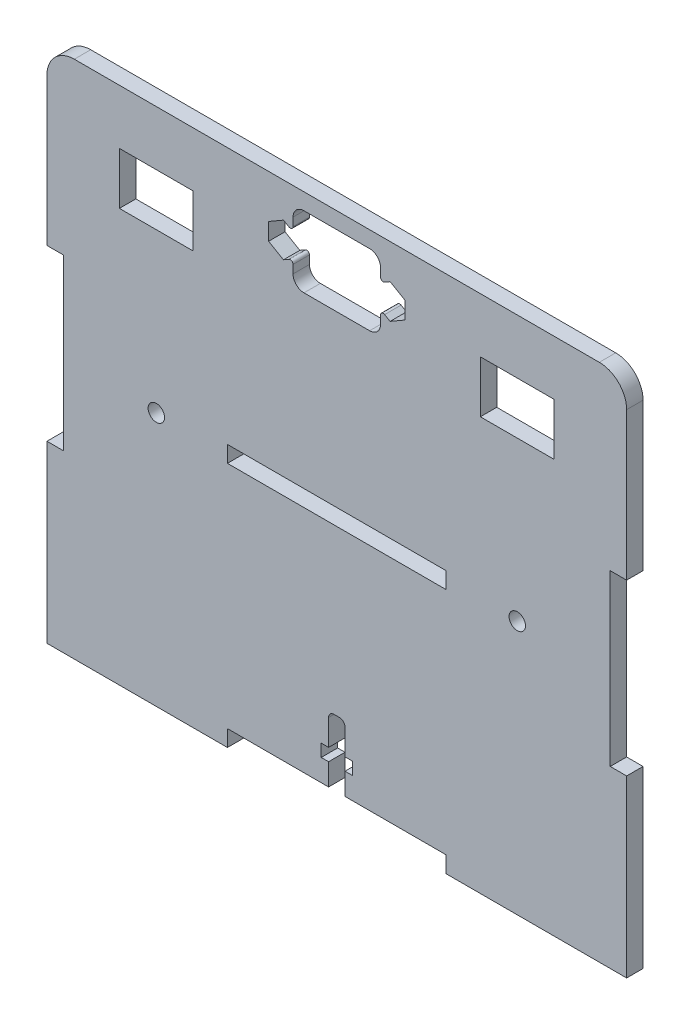
SolidWorks part; units mm, degrees
other "Marcação1"
sketch "Esboço7" plane through (-68, 31.5, 3) normal (-0.6758, 0.2828, 0.6807) x (0.7271, 0.1043, 0.6785)
sketch "Esboço8" plane through (-68, 31.5, 3) normal (-0.6758, 0.2828, 0.6807) x (0.7271, 0.1043, 0.6785)
sketch "Esboço9" plane through (-60.5, 31.5, 3) normal (-0.6758, 0.2828, 0.6807) x (0.7271, 0.1043, 0.6785)
sketch "Esboço12" plane through (-60.5, 31.5, 3) normal (-0.6758, 0.2828, 0.6807) x (0.7271, 0.1043, 0.6785)
sketch "Esboço14" plane through (-60.5, 31.5, 3) normal (-0.6758, 0.2828, 0.6807) x (0.7271, 0.1043, 0.6785)
sketch "Esboço15" plane through (-60.5, 36.25, 3) normal (-0.6758, 0.2828, 0.6807) x (0.7271, 0.1043, 0.6785)
sketch "Esboço18" plane through (-60.5, 33.25, 3) normal (-0.6758, 0.2828, 0.6807) x (0.7271, 0.1043, 0.6785)
sketch "Esboço20" plane through (-60.5, 29.8, 3) normal (-0.6758, 0.2828, 0.6807) x (0.7271, 0.1043, 0.6785)
sketch "Esboço22" plane through (-60.5, 29.8, 3) normal (-0.6758, 0.2828, 0.6807) x (0.7271, 0.1043, 0.6785)
material "Acrylic (Medium-high impact)"
ref_plane "Plano frontal" through (0, 0, 0) normal (0, 0, 1) x (1, 0, 0)
ref_plane "Plano superior" through (0, 0, 0) normal (0, 1, 0) x (1, 0, 0)
ref_plane "Plano direito" through (0, 0, 0) normal (1, 0, 0) x (0, 0, -1)
sketch "Esboço1" plane through (0, 0, 0) normal (0, 0, 1) x (1, 0, 0)
  line L1 (-50, -47.5) -> (50, -47.5)
  line L2 (-50, -47.5) -> (-50, 47.5)
  line L3 (-50, 47.5) -> (50, 47.5)
  line L4 (50, -47.5) -> (50, 47.5)
  line L5 (-50, -47.5) -> (50, 47.5) construction
  line L6 (-50, 47.5) -> (50, -47.5) construction
  point P0 (0, 0)
  dimension "D1" = 100
  dimension "D2" = 95
extrude "Ressalto-extrusão1" add sketch "Esboço1" along normal mid plane 3
sketch "Esboço3" plane through (0, 0, 1.5) normal (0, 0, 1) x (1, 0, 0)
  line L20 (50, 47.5) -> (-50, 47.5) construction
  line L21 (-53, 47.5) -> (-50, 47.5)
  line L22 (-53, 47.5) -> (-53, 15.5)
  line L23 (-53, 15.5) -> (-50, 15.5)
  line L24 (-50, 47.5) -> (-50, 15.5)
  line L25 (-50, 47.5) -> (-50, -47.5) construction
  line L26 (0, -1.65) -> (0, 1.65) construction
  line L27 (-50, -47.5) -> (-53, -47.5)
  line L28 (-50, -47.5) -> (-50, -15.5)
  line L29 (-50, -15.5) -> (-53, -15.5)
  line L30 (-53, -47.5) -> (-53, -15.5)
  line L31 (53, -47.5) -> (53, -15.5)
  line L32 (50, -15.5) -> (53, -15.5)
  line L33 (50, -47.5) -> (50, -15.5)
  line L34 (50, -47.5) -> (53, -47.5)
  line L35 (50, 47.5) -> (50, 15.5)
  line L36 (53, 15.5) -> (50, 15.5)
  line L37 (53, 47.5) -> (53, 15.5)
  line L38 (53, 47.5) -> (50, 47.5)
  dimension "D1" = 3
  dimension "D4" = 31
extrude "Ressalto-extrusão2" add sketch "Esboço3" against normal through all
sketch "Esboço2" plane through (0, 0, 1.5) normal (0, 0, 1) x (1, 0, 0)
  line L7 (-20, -47.5) -> (20, -47.5)
  line L15 (-20, -47.5) -> (-20, -44.5)
  line L21 (-20, 0.5) -> (20, 0.5)
  line L22 (-20, 0.5) -> (-20, -2.5)
  line L23 (-20, -2.5) -> (20, -2.5)
  line L24 (20, 0.5) -> (20, -2.5)
  line L25 (-20, 0.5) -> (20, -2.5) construction
  line L26 (-20, -2.5) -> (20, 0.5) construction
  line L27 (0, -1.65) -> (0, 1.65) construction
  line L28 (-53, -47.5) -> (53, -47.5) construction
  line L29 (-20, -44.5) -> (20, -44.5)
  line L30 (20, -47.5) -> (20, -44.5)
  circle A2 centre (-33, -1) radius 1.5
  circle A4 centre (33, -1) radius 1.5
  point P14 (0, -1)
  dimension "D4" = 13
  dimension "D8" = 3
  dimension "D2" = 3
  dimension "D3" = 45
  dimension "D6" = 3
  dimension "D13" = 40
extrude "Corte-extrusão1" cut sketch "Esboço2" against normal through all
sketch "Sketch9" plane through (0, 0, 0) normal (0, 0, 1) x (1, 0, 0)
  line L0 (20, -44.5) -> (-20, -44.5) construction
  line L1 (-1.5, -44.5) -> (1.5, -44.5)
  line L2 (-1.5, -44.5) -> (-1.5, -40.5)
  line L3 (-0.5, -32.5) -> (0.5, -32.5)
  line L4 (1.5, -44.5) -> (1.5, -40.5)
  line L5 (1.5, -38.23) -> (2.85, -38.23)
  line L6 (-2.85, -38.23) -> (-1.5, -38.23)
  line L7 (-2.85, -38.23) -> (-2.85, -40.5)
  line L8 (-2.85, -40.5) -> (-1.5, -40.5)
  line L9 (2.85, -38.23) -> (2.85, -40.5)
  line L10 (-1.5, -38.23) -> (-1.5, -33.5)
  line L11 (1.5, -40.5) -> (2.85, -40.5)
  line L12 (1.5, -38.23) -> (1.5, -33.5)
  arc A0 (0.5, -32.5) -> (1.5, -33.5) centre (0.5, -33.5) cw
  arc A1 (-1.5, -33.5) -> (-0.5, -32.5) centre (-0.5, -33.5) cw
  point P6 (0, -32.5)
  point P20 (-1.5, -32.5)
  dimension "D7" = 1
  dimension "D1" = 3
  dimension "D2" = 12
  dimension "D3" = 2.27
  dimension "D4" = 1.35
  dimension "D5" = 1.35
  dimension "D6" = 4
extrude "Cut-Extrude7" cut sketch "Sketch9" against normal through all both and the other way through all
sketch "Sketch6" plane through (0, 0, 0) normal (0, 0, 1) x (1, 0, 0)
  line L0 (0, 44.5) -> (0, 31.5) construction
  line L2 (-6, 44.5) -> (6, 44.5)
  line L3 (-8, 42.5) -> (-8, 41)
  line L4 (-6, 31.5) -> (6, 31.5)
  line L5 (8, 42.5) -> (8, 41)
  line L6 (53, 47.5) -> (-53, 47.5) construction
  line L7 (-9.75, 39.5) -> (-9.5, 39.5) construction
  line L9 (-9.75, 36.5) -> (-9.5, 36.5) construction
  line L11 (-8, 35) -> (-8, 33.5)
  line L12 (9.75, 39.5) -> (9.5, 39.5) construction
  line L13 (9.75, 36.5) -> (9.5, 36.5) construction
  line L14 (8, 35) -> (8, 33.5)
  line L15 (-53, 47.5) -> (-53, 15.5) construction
  line L16 (-9.75, 41.14) -> (-12.4693, 39.57)
  line L17 (-12.4693, 39.57) -> (-12.4693, 36.43)
  line L18 (-12.4693, 36.43) -> (-9.75, 34.86)
  line L19 (-9.75, 34.86) -> (-8.75, 35.4373)
  line L21 (-8.75, 40.5627) -> (-9.75, 41.14)
  line L22 (-7.0307, 36.43) -> (-7.0307, 38) [skipped]
  line L24 (9.75, 34.86) -> (12.4693, 36.43)
  line L25 (12.4693, 36.43) -> (12.4693, 39.57)
  line L26 (12.4693, 39.57) -> (9.75, 41.14)
  line L27 (9.75, 41.14) -> (8.75, 40.5627)
  line L29 (8.75, 35.4373) -> (9.75, 34.86)
  line L30 (7.0307, 39.57) -> (7.0307, 36.43) [skipped]
  arc A0 (-9.75, 39.5) -> (-9.75, 36.5) centre (-9.75, 38) ccw construction
  arc A1 (9.75, 36.5) -> (9.75, 39.5) centre (9.75, 38) ccw construction
  arc A2 (-8, 35.0065) -> (-8, 35) centre (-9.5, 35) cw
  arc A3 (-8, 40.9935) -> (-8, 41) centre (-9.5, 41) ccw
  arc A4 (6, 31.5) -> (8, 33.5) centre (6, 33.5) ccw
  arc A5 (-8, 33.5) -> (-6, 31.5) centre (-6, 33.5) ccw
  arc A6 (6, 44.5) -> (8, 42.5) centre (6, 42.5) cw
  arc A7 (-6, 44.5) -> (-8, 42.5) centre (-6, 42.5) ccw
  arc A8 (8, 35.0065) -> (8, 35) centre (9.5, 35) ccw
  arc A9 (8, 40.9935) -> (8, 41) centre (9.5, 41) cw
  arc A10 (-9.5, 36.5) -> (-8.2028, 35.7533) centre (-9.5, 35) cw construction
  arc A11 (-9.5, 39.5) -> (-8.2028, 40.2467) centre (-9.5, 41) ccw construction
  arc A12 (9.5, 36.5) -> (8.2028, 35.7533) centre (9.5, 35) ccw construction
  arc A13 (9.5, 39.5) -> (8.2028, 40.2467) centre (9.5, 41) cw construction
  arc A14 (8.75, 35.4373) -> (8, 35.0065) centre (8.5, 35.0043) ccw
  arc A15 (8.75, 40.5627) -> (8, 40.9935) centre (8.5, 40.9957) cw
  arc A16 (-8.75, 35.4373) -> (-8, 35.0065) centre (-8.5, 35.0043) cw
  arc A17 (-8.75, 40.5627) -> (-8, 40.9935) centre (-8.5, 40.9957) ccw
  point P7 (0, 31.5)
  point P19 (-8, 36.5)
  point P26 (-8, 31.5)
  point P29 (8, 44.5)
  point P32 (-8, 44.5)
  point P37 (8, 36.5)
  dimension "D4" = 19.5
  dimension "D7" = 2
  dimension "D8" = 5
  dimension "D5" = 3
  dimension "D6" = 1.5
  dimension "D9" = 1.5
  dimension "D11" = 0.5
  dimension "D1" = 16
  dimension "D2" = 3
  dimension "D3" = 13
  dimension "D10" = 3.14
extrude "Cut-Extrude5" cut sketch "Sketch6" against normal through all both and the other way through all
sketch "Sketch7" plane through (0, 0, 0) normal (0, 0, 1) x (1, 0, 0)
  line L0 (-53, 47.5) -> (-53, 15.5) construction
  line L1 (-39.75, 37.5) -> (-26.25, 37.5)
  line L2 (-39.75, 37.5) -> (-39.75, 28)
  line L3 (-39.75, 28) -> (-26.25, 28)
  line L4 (-26.25, 37.5) -> (-26.25, 28)
  line L5 (0, -1.65) -> (0, 1.65) construction
  line L9 (26.25, 37.5) -> (26.25, 28)
  line L10 (39.75, 28) -> (26.25, 28)
  line L11 (39.75, 37.5) -> (39.75, 28)
  line L12 (39.75, 37.5) -> (26.25, 37.5)
  line L13 (53, 47.5) -> (-53, 47.5) construction
  dimension "D1" = 13.5
  dimension "D2" = 9.5
  dimension "D3" = 10
  dimension "D4" = 13.25
extrude "Cut-Extrude6" cut sketch "Sketch7" against normal through all both and the other way through all
fillet "Fillet2" radius 5 2 edges at (53, 47.5, 0) (-53, 47.5, 0)
